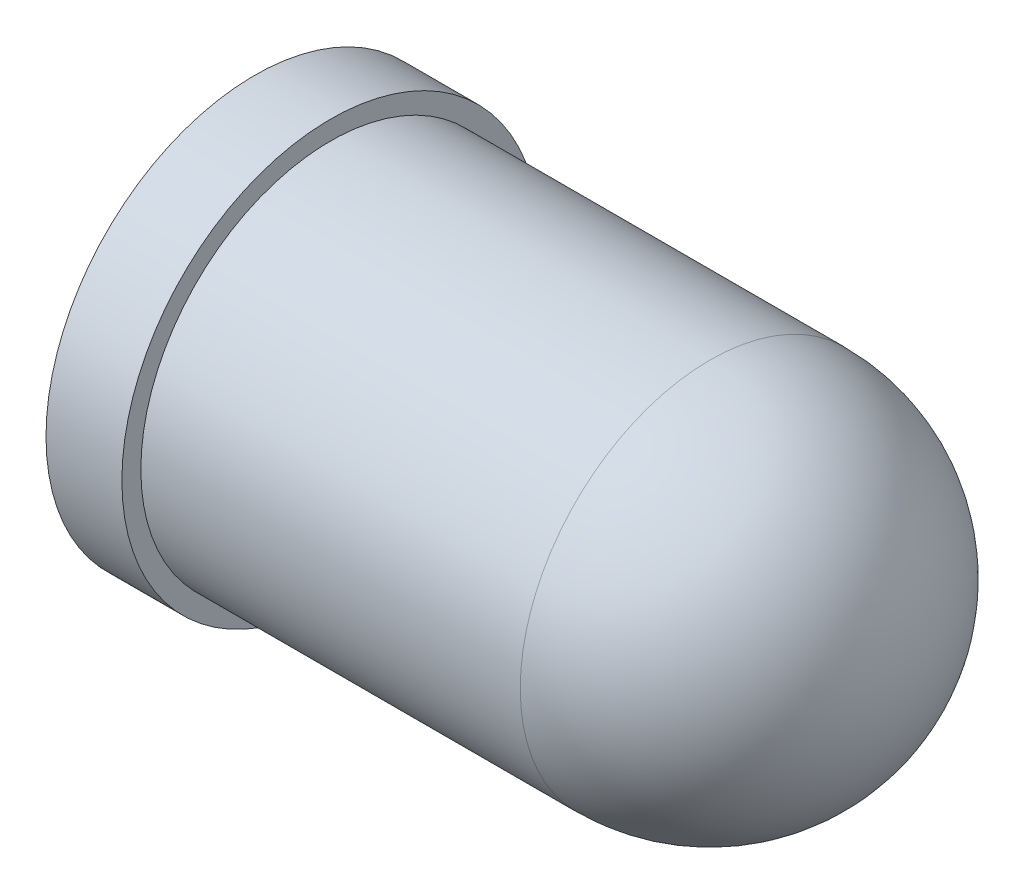
SolidWorks part; units mm, degrees
ref_plane "Front Plane" through (0, 0, 0) normal (0, 0, 1) x (1, 0, 0)
ref_plane "Top Plane" through (0, 0, 0) normal (0, 1, 0) x (1, 0, 0)
ref_plane "Right Plane" through (0, 0, 0) normal (1, 0, 0) x (0, 0, -1)
sketch "Sketch1" plane through (0, 0, 0) normal (0, 0, 1) x (1, 0, 0)
  line L0 (0, 2.5) -> (-5, 2.5)
  line L1 (-5, 2.5) -> (-5, 2.75)
  line L2 (-5, 2.75) -> (-6, 2.75)
  line L3 (-6, 2.75) -> (-6, 0)
  line L4 (-6, 0) -> (2.5, 0)
  arc A0 (2.5, 0) -> (0, 2.5) centre (0, 0) ccw
  dimension "D1" = 2.5
  dimension "D2" = 7.5
  dimension "D3" = 1
  dimension "D4" = 2.75
revolve "Revolve1" add sketch "Sketch1" angle 360 about L4
